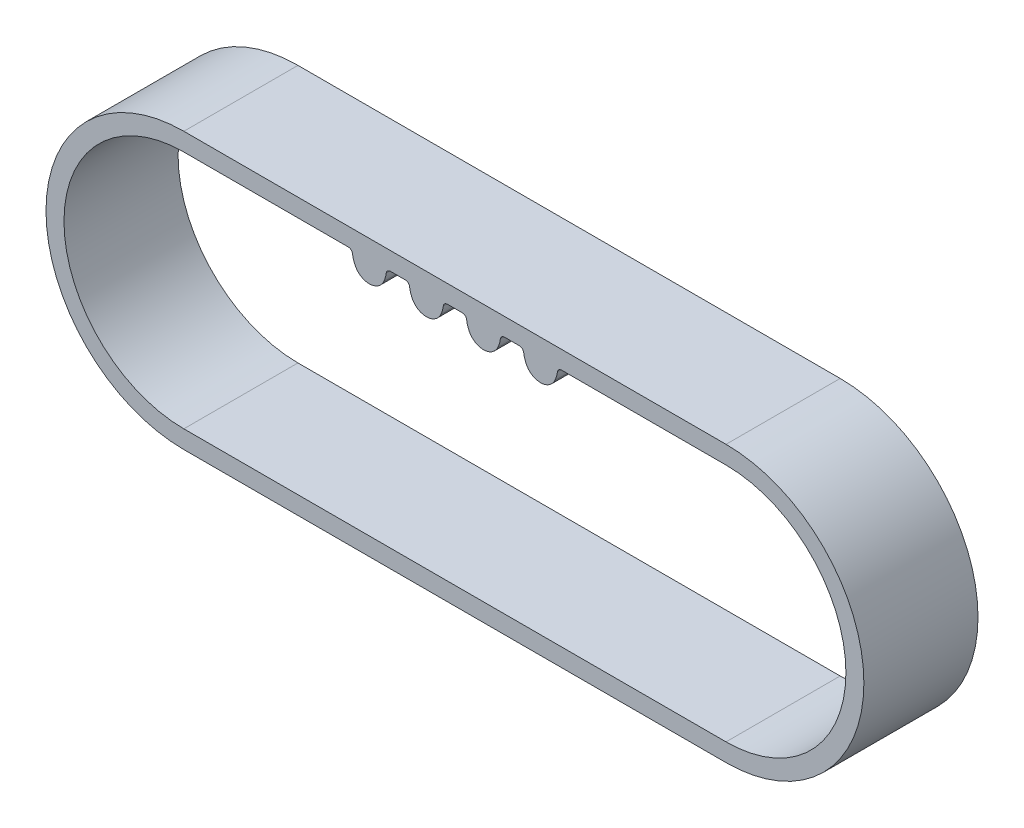
SolidWorks part; units mm, degrees
material "クロロプレンゴム"
ref_plane "Front Plane" through (0, 0, 0) normal (0, 0, 1) x (1, 0, 0)
ref_plane "Top Plane" through (0, 0, 0) normal (0, 1, 0) x (1, 0, 0)
ref_plane "Right Plane" through (0, 0, 0) normal (1, 0, 0) x (0, 0, -1)
sketch "Sketch1" plane through (0, 0, 0) normal (0, 0, 1) x (1, 0, 0)
  line L0 (0, 4.201) -> (19.0042, 4.201)
  line L1 (0, -4.201) -> (19.0042, -4.201)
  line L2 (0, 0) -> (19.0042, 0) construction
  line L3 (0, 4.455) -> (19.0042, 4.455) construction
  line L4 (0, -4.455) -> (19.0042, -4.455) construction
  line L5 (0, 4.831) -> (19.0042, 4.831)
  line L6 (0, -4.831) -> (19.0042, -4.831)
  arc A0 (0, 4.455) -> (0, -4.455) centre (0, 0) ccw construction
  arc A1 (19.0042, -4.455) -> (19.0042, 4.455) centre (19.0042, 0) ccw construction
  arc A2 (0, -4.201) -> (0, 4.201) centre (0, 0) cw
  arc A3 (19.0042, 4.201) -> (19.0042, -4.201) centre (19.0042, 0) cw
  arc A4 (0, 4.831) -> (0, -4.831) centre (0, 0) ccw
  arc A5 (19.0042, -4.831) -> (19.0042, 4.831) centre (19.0042, 0) ccw
  dimension "D35" = 8.91
  dimension "I_s" = 0.63
  dimension "D1" = 19.0042
  dimension "PLD" = 0.254
extrude "Boss-Extrude1" add sketch "Sketch1" along normal mid plane 4
sketch "Sketch2" plane through (0, 0, 0) normal (0, 0, 1) x (1, 0, 0)
  line L0 (5.5021, 4.831) -> (5.5021, 4.201)
  line L1 (9.5021, 4.831) -> (9.5021, 4.201)
  line L2 (7.2423, 4.201) -> (7.7619, 4.201)
  line L3 (9.5021, 4.831) -> (5.5021, 4.831)
  line L5 (6.5021, 3.451) -> (6.5021, 4.831) construction
  line L6 (8.5021, 3.451) -> (8.5021, 4.831) construction
  line L8 (0, 4.831) -> (19.0042, 4.831) construction
  line L9 (0, 4.201) -> (19.0042, 4.201) construction
  line L10 (9.5021, 4.201) -> (9.2423, 4.201)
  line L12 (5.7619, 4.201) -> (5.5021, 4.201)
  arc A0 (5.7619, 4.201) -> (5.9106, 4.0706) centre (5.7619, 4.051) cw
  arc A1 (5.9106, 4.0706) -> (6.0032, 3.7628) centre (6.9021, 4.201) ccw
  arc A2 (6.0032, 3.7628) -> (7.001, 3.7628) centre (6.5021, 4.006) ccw
  arc A3 (7.001, 3.7628) -> (7.0936, 4.0706) centre (6.1021, 4.201) ccw
  arc A4 (7.0936, 4.0706) -> (7.2423, 4.201) centre (7.2423, 4.051) cw
  arc A5 (7.7619, 4.201) -> (7.9106, 4.0706) centre (7.7619, 4.051) cw
  arc A6 (7.9106, 4.0706) -> (8.0032, 3.7628) centre (8.9021, 4.201) ccw
  arc A7 (8.0032, 3.7628) -> (9.001, 3.7628) centre (8.5021, 4.006) ccw
  arc A8 (9.001, 3.7628) -> (9.0936, 4.0706) centre (8.1021, 4.201) ccw
  arc A9 (9.0936, 4.0706) -> (9.2423, 4.201) centre (9.2423, 4.051) cw
  point P26 (7.5021, 4.201)
  dimension "D1" = 1
  dimension "R1" = 0.15
  dimension "R2" = 1
  dimension "R3" = 0.555
  dimension "I_s" = 0.63
  dimension "Pitch" = 2
  dimension "H" = 1.38
  dimension "B_s" = 0.4
extrude "Boss-Extrude2" add sketch "Sketch2" along normal through all and the other way through all
pattern_linear "LPattern1" count 2 spacing 4 along (1, 0, 0) of "Boss-Extrude2"
equation "\"Teeth\"= 33"
equation "\"D1@Sketch1\"= ( ( \"Teeth\" * \"Pitch\" ) - ( \"D35@Sketch1\" * PI ) ) / 2"
equation "\"Pitch\"=2"
equation "\"Pitch@Sketch2\" = \"Pitch\""
equation "\"D3@LPattern1\" = \"Pitch\" * 2"
